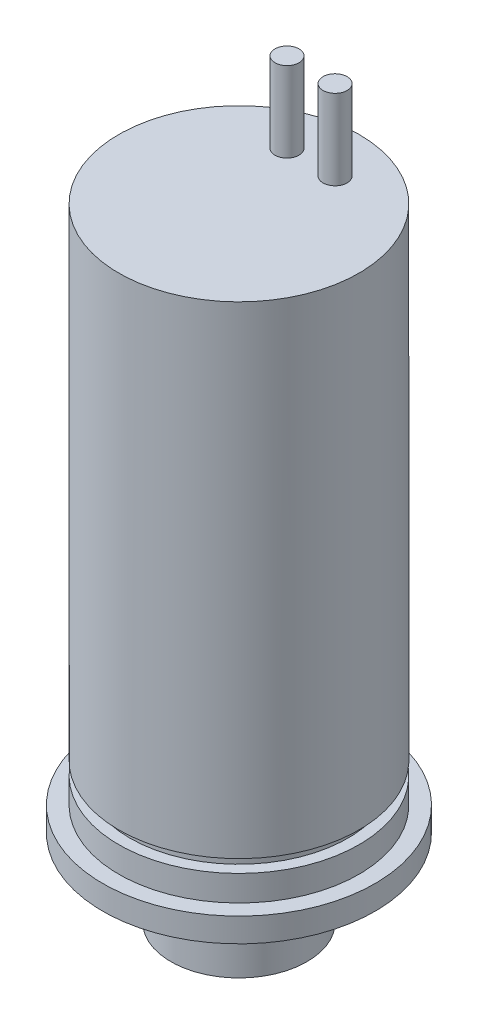
SolidWorks part; units mm, degrees
material "Plain Carbon Steel"
ref_plane "Front Plane" through (0, 0, 0) normal (0, 0, 1) x (1, 0, 0)
ref_plane "Top Plane" through (0, 0, 0) normal (0, 1, 0) x (1, 0, 0)
ref_plane "Right Plane" through (0, 0, 0) normal (1, 0, 0) x (0, 0, -1)
sketch "Sketch1" plane through (0, 0, 0) normal (0, 0, 1) x (1, 0, 0)
  line L0 (0, 0) -> (-4.25, 0)
  line L1 (-4.25, 0) -> (-4.25, 5.5)
  line L2 (-4.25, 5.5) -> (-8.5, 5.5)
  line L3 (-8.5, 5.5) -> (-8.5, 7)
  line L4 (-8.5, 7) -> (-7.5, 7)
  line L5 (-7.5, 7) -> (-7.5, 39.5)
  line L6 (-7.5, 39.5) -> (0, 39.5)
  line L7 (0, 0) -> (0, 39.5)
  line L8 (7.5, 39.5) -> (0, 39.5) construction
  line L9 (7.5, 7) -> (7.5, 39.5) construction
  line L10 (8.5, 7) -> (7.5, 7) construction
  line L11 (8.5, 5.5) -> (8.5, 7) construction
  line L12 (4.25, 5.5) -> (8.5, 5.5) construction
  line L13 (4.25, 0) -> (4.25, 5.5) construction
  line L14 (0, 0) -> (4.25, 0) construction
  point P15 (-8.5, 6.25)
  dimension "D1" = 8.5
  dimension "D2" = 17
  dimension "D3" = 15
  dimension "D4" = 32.5
  dimension "D5" = 34
  dimension "D6" = 39.5
revolve "Revolve2" add sketch "Sketch1" angle 360 about L7
sketch "Sketch2" plane through (0, 39.5, 0) normal (0, 1, 0) x (1, 0, 0)
  line L0 (0, -7.5) -> (0, 7.5) construction
  circle A0 centre (0, 0) radius 7.5 construction
  circle A1 centre (0, 0) radius 7.5 construction
  circle A2 centre (1.5, 4.5) radius 0.75
  circle A3 centre (-1.5, 4.5) radius 0.75
  dimension "D3" = 1.5
  dimension "D1" = 3
  dimension "D2" = 3
extrude "Boss-Extrude1" add sketch "Sketch2" along normal blind 5
sketch "Sketch3" plane through (0, 0, 0) normal (1, 0, 0) x (0, 0, -1)
  line L6 (0, 0) -> (0, 5.5) construction
  line L7 (-4.25, 5.5) -> (4.25, 5.5) construction
  line L8 (-4.25, 0) -> (4.25, 0) construction
  line L9 (4.25, 0) -> (3.26, 0)
  line L10 (4.25, 0) -> (4.25, 0.65)
  line L11 (4.25, 0.65) -> (3.26, 0.65)
  line L12 (3.26, 0) -> (3.26, 0.65)
  line L13 (4.25, 0) -> (4.25, 5.5) construction
  dimension "D1" = 0.65
  dimension "D2" = 6.52
revolve "Cut-Revolve1" cut sketch "Sketch3" angle 360 about L6
sketch "Sketch4" plane through (0, 0, 0) normal (0, -1, 0) x (1, 0, 0)
  circle A0 centre (0, 0) radius 1.17
  dimension "D1" = 2.34
extrude "Cut-Extrude1" cut sketch "Sketch4" against normal blind 7.5
sketch "Sketch5" plane through (0, 0, 0) normal (1, 0, 0) x (0, 0, -1)
  line L0 (-8.5, 5.5) -> (8.5, 5.5) construction
  line L1 (7.63, 5.5) -> (6.5, 5.5)
  line L2 (7.63, 5.5) -> (7.63, 6.4)
  line L3 (7.63, 6.4) -> (6.5, 6.4)
  line L4 (6.5, 5.5) -> (6.5, 6.4)
  line L5 (0, 0) -> (0, 7) construction
  line L6 (8.5, 7) -> (-8.5, 7) construction
  point P11 (7.065, 5.5)
  dimension "D1" = 13
  dimension "D2" = 15.26
  dimension "D3" = 0.9
revolve "Cut-Revolve2" cut sketch "Sketch5" angle 360 about L5
sketch "N" plane through (0, 0, 0) normal (1, 0, 0) x (0, 0, -1)
  line L1 (7.6, 8.6) -> (6.8, 8.6)
  line L2 (7.6, 8.6) -> (7.6, 9.4)
  line L3 (7.6, 9.4) -> (6.8, 9.4)
  line L4 (6.8, 8.6) -> (6.8, 9.4)
  line L5 (0, 0) -> (0, 14.7925) construction
  line L6 (-3.26, 0) -> (3.26, 0) construction
  line L7 (7.5, 7) -> (7.5, 39.5) construction
  point P6 (7.6, 9)
  dimension "D1" = 0.8
  dimension "D2" = 3.5
  dimension "D3" = 0.8
  dimension "D4" = 0.1
revolve "Cut-Revolve8" cut sketch "N" angle 360 about L5
